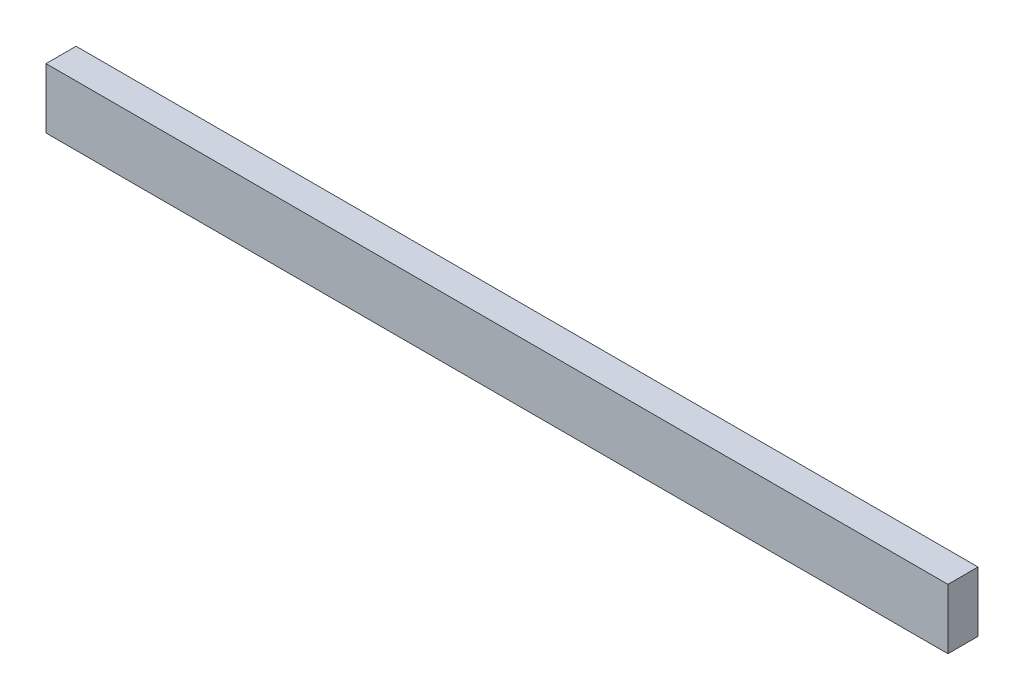
SolidWorks part; units mm, degrees
ref_plane "Front Plane" through (0, 0, 0) normal (0, 0, 1) x (1, 0, 0)
ref_plane "Top Plane" through (0, 0, 0) normal (0, 1, 0) x (1, 0, 0)
ref_plane "Right Plane" through (0, 0, 0) normal (1, 0, 0) x (0, 0, -1)
sketch "Sketch1" plane through (0, 0, 0) normal (0, 0, 1) x (1, 0, 0)
  line L1 (-15, 1) -> (15, 1)
  line L2 (-15, 1) -> (-15, -1)
  line L3 (-15, -1) -> (15, -1)
  line L4 (15, 1) -> (15, -1)
  line L5 (-15, 1) -> (15, -1) construction
  line L6 (-15, -1) -> (15, 1) construction
  point P0 (0, 0)
  dimension "D1" = 30
  dimension "D2" = 2
extrude "Boss-Extrude1" add sketch "Sketch1" along normal blind 1
